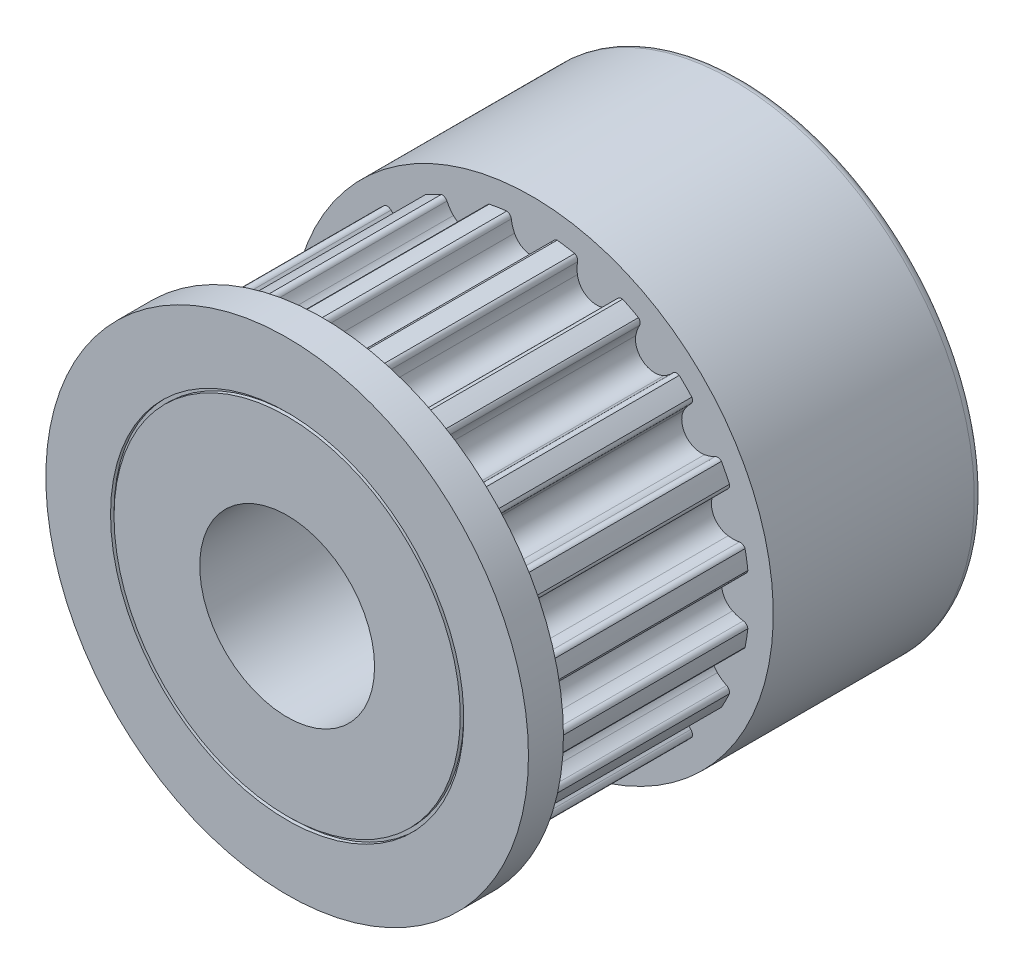
SolidWorks part; units mm, degrees
ref_plane "Piano frontale" through (0, 0, 0) normal (0, 0, 1) x (1, 0, 0)
ref_plane "Piano superiore" through (0, 0, 0) normal (0, 1, 0) x (1, 0, 0)
ref_plane "Piano destro" through (0, 0, 0) normal (1, 0, 0) x (0, 0, -1)
sketch "Schizzo1" plane through (0, 0, 0) normal (0, 1, 0) x (1, 0, 0)
  line L0 (6.9, -17) -> (0, -17)
  line L1 (0, -17) -> (0, -18)
  line L2 (0, -18) -> (6.9, -18)
  line L3 (6.9, -18) -> (6.9, -17)
  line L4 (0, -17) -> (0, -18) construction
revolve "Rivoluzione1" add sketch "Schizzo1" angle 360 about L4
sketch "Schizzo2" plane through (0, 0, 17) normal (0, 0, -1) x (-1, 0, 0)
  arc A0 (5.4177, -3.0455) -> (5.2373, -3.074) centre (5.3089, -2.9422) cw
  arc A1 (5.2373, -3.074) -> (4.9339, -2.968) centre (4.7601, -3.9528) ccw
  arc A2 (4.9339, -2.968) -> (4.3474, -3.7752) centre (4.8374, -3.5146) ccw
  arc A3 (4.3474, -3.7752) -> (4.542, -4.031) centre (5.2303, -3.3056) ccw
  arc A4 (4.542, -4.031) -> (4.5706, -4.2114) centre (4.4388, -4.1399) cw
  arc A5 (4.5706, -4.2114) -> (4.2114, -4.5706) centre (0, 0) cw
  arc A6 (4.2114, -4.5706) -> (4.031, -4.542) centre (4.1399, -4.4388) cw
  arc A7 (4.031, -4.542) -> (3.7752, -4.3474) centre (3.3056, -5.2303) ccw
  arc A8 (3.7752, -4.3474) -> (2.968, -4.9339) centre (3.5146, -4.8374) ccw
  arc A9 (2.968, -4.9339) -> (3.074, -5.2373) centre (3.9528, -4.7601) ccw
  arc A10 (3.074, -5.2373) -> (3.0455, -5.4177) centre (2.9422, -5.3089) cw
  arc A11 (3.0455, -5.4177) -> (2.5929, -5.6483) centre (0, 0) cw
  arc A12 (2.5929, -5.6483) -> (2.4302, -5.5654) centre (2.5656, -5.5008) cw
  arc A13 (2.4302, -5.5654) -> (2.247, -5.3013) centre (1.5276, -5.9958) ccw
  arc A14 (2.247, -5.3013) -> (1.2981, -5.6096) centre (1.8477, -5.6867) ccw
  arc A15 (1.2981, -5.6096) -> (1.3052, -5.9309) centre (2.2884, -5.7486) ccw
  arc A16 (1.3052, -5.9309) -> (1.2223, -6.0936) centre (1.1577, -5.9582) cw
  arc A17 (1.2223, -6.0936) -> (0.7206, -6.1731) centre (0, 0) cw
  arc A18 (0.7206, -6.1731) -> (0.5915, -6.0439) centre (0.7402, -6.0244) cw
  arc A19 (0.5915, -6.0439) -> (0.4989, -5.7362) centre (-0.4, -6.1744) ccw
  arc A20 (0.4989, -5.7362) -> (-0.4989, -5.7362) centre (0, -5.9794) ccw
  arc A21 (-0.4989, -5.7362) -> (-0.5915, -6.0439) centre (0.4, -6.1744) ccw
  arc A22 (-0.5915, -6.0439) -> (-0.7206, -6.1731) centre (-0.7402, -6.0244) cw
  arc A23 (-0.7206, -6.1731) -> (-1.2223, -6.0936) centre (0, 0) cw
  arc A24 (-1.2223, -6.0936) -> (-1.3052, -5.9309) centre (-1.1577, -5.9582) cw
  arc A25 (-1.3052, -5.9309) -> (-1.2981, -5.6096) centre (-2.2884, -5.7486) ccw
  arc A26 (-1.2981, -5.6096) -> (-2.247, -5.3013) centre (-1.8477, -5.6867) ccw
  arc A27 (-2.247, -5.3013) -> (-2.4302, -5.5654) centre (-1.5276, -5.9958) ccw
  arc A28 (-2.4302, -5.5654) -> (-2.5929, -5.6483) centre (-2.5656, -5.5008) cw
  arc A29 (-2.5929, -5.6483) -> (-3.0455, -5.4177) centre (0, 0) cw
  arc A30 (-3.0455, -5.4177) -> (-3.074, -5.2373) centre (-2.9422, -5.3089) cw
  arc A31 (-3.074, -5.2373) -> (-2.968, -4.9339) centre (-3.9528, -4.7601) ccw
  arc A32 (-2.968, -4.9339) -> (-3.7752, -4.3474) centre (-3.5146, -4.8374) ccw
  arc A33 (-3.7752, -4.3474) -> (-4.031, -4.542) centre (-3.3056, -5.2303) ccw
  arc A34 (-4.031, -4.542) -> (-4.2114, -4.5706) centre (-4.1399, -4.4388) cw
  arc A35 (-4.2114, -4.5706) -> (-4.5706, -4.2114) centre (0, 0) cw
  arc A36 (-4.5706, -4.2114) -> (-4.542, -4.031) centre (-4.4388, -4.1399) cw
  arc A37 (-4.542, -4.031) -> (-4.3474, -3.7752) centre (-5.2303, -3.3056) ccw
  arc A38 (-4.3474, -3.7752) -> (-4.9339, -2.968) centre (-4.8374, -3.5146) ccw
  arc A39 (-4.9339, -2.968) -> (-5.2373, -3.074) centre (-4.7601, -3.9528) ccw
  arc A40 (-5.2373, -3.074) -> (-5.4177, -3.0455) centre (-5.3089, -2.9422) cw
  arc A41 (-5.4177, -3.0455) -> (-5.6483, -2.5929) centre (0, 0) cw
  arc A42 (-5.6483, -2.5929) -> (-5.5654, -2.4302) centre (-5.5008, -2.5656) cw
  arc A43 (-5.5654, -2.4302) -> (-5.3013, -2.247) centre (-5.9958, -1.5276) ccw
  arc A44 (-5.3013, -2.247) -> (-5.6096, -1.2981) centre (-5.6867, -1.8477) ccw
  arc A45 (-5.6096, -1.2981) -> (-5.9309, -1.3052) centre (-5.7486, -2.2884) ccw
  arc A46 (-5.9309, -1.3052) -> (-6.0936, -1.2223) centre (-5.9582, -1.1577) cw
  arc A47 (-6.0936, -1.2223) -> (-6.1731, -0.7206) centre (0, 0) cw
  arc A48 (-6.1731, -0.7206) -> (-6.0439, -0.5915) centre (-6.0244, -0.7402) cw
  arc A49 (-6.0439, -0.5915) -> (-5.7362, -0.4989) centre (-6.1744, 0.4) ccw
  arc A50 (-5.7362, -0.4989) -> (-5.7362, 0.4989) centre (-5.9794, 0) ccw
  arc A51 (-5.7362, 0.4989) -> (-6.0439, 0.5915) centre (-6.1744, -0.4) ccw
  arc A52 (-6.0439, 0.5915) -> (-6.1731, 0.7206) centre (-6.0244, 0.7402) cw
  arc A53 (-6.1731, 0.7206) -> (-6.0936, 1.2223) centre (0, 0) cw
  arc A54 (-6.0936, 1.2223) -> (-5.9309, 1.3052) centre (-5.9582, 1.1577) cw
  arc A55 (-5.9309, 1.3052) -> (-5.6096, 1.2981) centre (-5.7486, 2.2884) ccw
  arc A56 (-5.6096, 1.2981) -> (-5.3013, 2.247) centre (-5.6867, 1.8477) ccw
  arc A57 (-5.3013, 2.247) -> (-5.5654, 2.4302) centre (-5.9958, 1.5276) ccw
  arc A58 (-5.5654, 2.4302) -> (-5.6483, 2.5929) centre (-5.5008, 2.5656) cw
  arc A59 (-5.6483, 2.5929) -> (-5.4177, 3.0455) centre (0, 0) cw
  arc A60 (-5.4177, 3.0455) -> (-5.2373, 3.074) centre (-5.3089, 2.9422) cw
  arc A61 (-5.2373, 3.074) -> (-4.9339, 2.968) centre (-4.7601, 3.9528) ccw
  arc A62 (-4.9339, 2.968) -> (-4.3474, 3.7752) centre (-4.8374, 3.5146) ccw
  arc A63 (-4.3474, 3.7752) -> (-4.542, 4.031) centre (-5.2303, 3.3056) ccw
  arc A64 (-4.542, 4.031) -> (-4.5706, 4.2114) centre (-4.4388, 4.1399) cw
  arc A65 (-4.5706, 4.2114) -> (-4.2114, 4.5706) centre (0, 0) cw
  arc A66 (-4.2114, 4.5706) -> (-4.031, 4.542) centre (-4.1399, 4.4388) cw
  arc A67 (-4.031, 4.542) -> (-3.7752, 4.3474) centre (-3.3056, 5.2303) ccw
  arc A68 (-3.7752, 4.3474) -> (-2.968, 4.9339) centre (-3.5146, 4.8374) ccw
  arc A69 (-2.968, 4.9339) -> (-3.074, 5.2373) centre (-3.9528, 4.7601) ccw
  arc A70 (-3.074, 5.2373) -> (-3.0455, 5.4177) centre (-2.9422, 5.3089) cw
  arc A71 (-3.0455, 5.4177) -> (-2.5929, 5.6483) centre (0, 0) cw
  arc A72 (-2.5929, 5.6483) -> (-2.4302, 5.5654) centre (-2.5656, 5.5008) cw
  arc A73 (-2.4302, 5.5654) -> (-2.247, 5.3013) centre (-1.5276, 5.9958) ccw
  arc A74 (-2.247, 5.3013) -> (-1.2981, 5.6096) centre (-1.8477, 5.6867) ccw
  arc A75 (-1.2981, 5.6096) -> (-1.3052, 5.9309) centre (-2.2884, 5.7486) ccw
  arc A76 (-1.3052, 5.9309) -> (-1.2223, 6.0936) centre (-1.1577, 5.9582) cw
  arc A77 (-1.2223, 6.0936) -> (-0.7206, 6.1731) centre (0, 0) cw
  arc A78 (-0.7206, 6.1731) -> (-0.5915, 6.0439) centre (-0.7402, 6.0244) cw
  arc A79 (-0.5915, 6.0439) -> (-0.4989, 5.7362) centre (0.4, 6.1744) ccw
  arc A80 (-0.4989, 5.7362) -> (0.4989, 5.7362) centre (0, 5.9794) ccw
  arc A81 (0.4989, 5.7362) -> (0.5915, 6.0439) centre (-0.4, 6.1744) ccw
  arc A82 (0.5915, 6.0439) -> (0.7206, 6.1731) centre (0.7402, 6.0244) cw
  arc A83 (0.7206, 6.1731) -> (1.2223, 6.0936) centre (0, 0) cw
  arc A84 (1.2223, 6.0936) -> (1.3052, 5.9309) centre (1.1577, 5.9582) cw
  arc A85 (1.3052, 5.9309) -> (1.2981, 5.6096) centre (2.2884, 5.7486) ccw
  arc A86 (1.2981, 5.6096) -> (2.247, 5.3013) centre (1.8477, 5.6867) ccw
  arc A87 (2.247, 5.3013) -> (2.4302, 5.5654) centre (1.5276, 5.9958) ccw
  arc A88 (2.4302, 5.5654) -> (2.5929, 5.6483) centre (2.5656, 5.5008) cw
  arc A89 (2.5929, 5.6483) -> (3.0455, 5.4177) centre (0, 0) cw
  arc A90 (3.0455, 5.4177) -> (3.074, 5.2373) centre (2.9422, 5.3089) cw
  arc A91 (3.074, 5.2373) -> (2.968, 4.9339) centre (3.9528, 4.7601) ccw
  arc A92 (2.968, 4.9339) -> (3.7752, 4.3474) centre (3.5146, 4.8374) ccw
  arc A93 (3.7752, 4.3474) -> (4.031, 4.542) centre (3.3056, 5.2303) ccw
  arc A94 (4.031, 4.542) -> (4.2114, 4.5706) centre (4.1399, 4.4388) cw
  arc A95 (4.2114, 4.5706) -> (4.5706, 4.2114) centre (0, 0) cw
  arc A96 (4.5706, 4.2114) -> (4.542, 4.031) centre (4.4388, 4.1399) cw
  arc A97 (4.542, 4.031) -> (4.3474, 3.7752) centre (5.2303, 3.3056) ccw
  arc A98 (4.3474, 3.7752) -> (4.9339, 2.968) centre (4.8374, 3.5146) ccw
  arc A99 (4.9339, 2.968) -> (5.2373, 3.074) centre (4.7601, 3.9528) ccw
  arc A100 (5.2373, 3.074) -> (5.4177, 3.0455) centre (5.3089, 2.9422) cw
  arc A101 (5.4177, 3.0455) -> (5.6483, 2.5929) centre (0, 0) cw
  arc A102 (5.6483, 2.5929) -> (5.5654, 2.4302) centre (5.5008, 2.5656) cw
  arc A103 (5.5654, 2.4302) -> (5.3013, 2.247) centre (5.9958, 1.5276) ccw
  arc A104 (5.3013, 2.247) -> (5.6096, 1.2981) centre (5.6867, 1.8477) ccw
  arc A105 (5.6096, 1.2981) -> (5.9309, 1.3052) centre (5.7486, 2.2884) ccw
  arc A106 (5.9309, 1.3052) -> (6.0936, 1.2223) centre (5.9582, 1.1577) cw
  arc A107 (6.0936, 1.2223) -> (6.1731, 0.7206) centre (0, 0) cw
  arc A108 (6.1731, 0.7206) -> (6.0439, 0.5915) centre (6.0244, 0.7402) cw
  arc A109 (6.0439, 0.5915) -> (5.7362, 0.4989) centre (6.1744, -0.4) ccw
  arc A110 (5.7362, 0.4989) -> (5.7362, -0.4989) centre (5.9794, 0) ccw
  arc A111 (5.7362, -0.4989) -> (6.0439, -0.5915) centre (6.1744, 0.4) ccw
  arc A112 (6.0439, -0.5915) -> (6.1731, -0.7206) centre (6.0244, -0.7402) cw
  arc A113 (6.1731, -0.7206) -> (6.0936, -1.2223) centre (0, 0) cw
  arc A114 (6.0936, -1.2223) -> (5.9309, -1.3052) centre (5.9582, -1.1577) cw
  arc A115 (5.9309, -1.3052) -> (5.6096, -1.2981) centre (5.7486, -2.2884) ccw
  arc A116 (5.6096, -1.2981) -> (5.3013, -2.247) centre (5.6867, -1.8477) ccw
  arc A117 (5.3013, -2.247) -> (5.5654, -2.4302) centre (5.9958, -1.5276) ccw
  arc A118 (5.5654, -2.4302) -> (5.6483, -2.5929) centre (5.5008, -2.5656) cw
  arc A119 (5.6483, -2.5929) -> (5.4177, -3.0455) centre (0, 0) cw
extrude "Estrusione-Estrusione1" add sketch "Schizzo2" along normal blind 6
ref_plane "Piano1" through (0, 0, 6) normal (0, 0, 1) x (1, 0, 0)
sketch "Schizzo3" plane through (0, 0, 11) normal (0, 0, 1) x (1, 0, 0)
  circle A0 centre (0, 0) radius 6.9
extrude "Estrusione-Estrusione2" add sketch "Schizzo3" against normal blind 6
sketch "Schizzo4" plane through (0, 0, 18) normal (0, 0, 1) x (1, 0, 0)
  circle A0 centre (0, 0) radius 5.05
extrude "Taglio-Estrusione1" cut sketch "Schizzo4" against normal blind 0.1
sketch "Schizzo5" plane through (0, 0, 17.9) normal (0, 0, 1) x (1, 0, 0)
  circle A0 centre (0, 0) radius 4.95
extrude "Estrusione-Estrusione3" add sketch "Schizzo5" along normal blind 0.1
hole_wizard "Foro1" positions "Schizzo7" profile "Schizzo6" legacy
sketch "Schizzo7" plane through (0, 0, 5) normal (0, 0, -1) x (-1, 0, 0)
  point P0 (0, 0)
sketch "Schizzo6" plane through (0, 0, 5) normal (1, 0, 0) x (0, 1, 0)
  line L0 (0, 0) -> (0, 0.1)
  line L1 (0, 0.1) -> (5.05, 0.1)
  line L2 (5.05, 0.1) -> (5.05, 0)
  line L3 (5.05, 0) -> (0, 0)
  line L4 (0, 110) -> (0, -10) construction
  dimension "Diameter" = 10.1
  dimension "Depth" = 0.1
sketch "Schizzo8" plane through (0, 0, 5.1) normal (0, 0, -1) x (-1, 0, 0)
  circle A0 centre (0, 0) radius 4.95
extrude "Estrusione-Estrusione4" add sketch "Schizzo8" along normal blind 0.1
hole_wizard "Foro Ø5.0 (5)-1" positions "Schizzo10" profile "Schizzo9" hole size "Ø5.0" standard "Ansi Metric"
sketch "Schizzo10" plane through (0, 0, 18) normal (0, 0, 1) x (1, 0, 0)
  point P0 (0, 0)
sketch "Schizzo9" plane through (0, 0, 18) normal (1, 0, 0) x (0, -1, 0)
  line L0 (0, 0) -> (0, 13)
  line L1 (0, 13) -> (2.5, 13)
  line L2 (2.5, 13) -> (2.5, 0)
  line L5 (2.5, 0) -> (0, 0)
  line L11 (0, -6.35) -> (0, 107.95) construction
  dimension "Thru Hole Dia." = 5
  dimension "Thru Hole Depth" = 13
fillet "Raccordo1" radius 0.25 1 edges at (-6.9, 0, 5)
